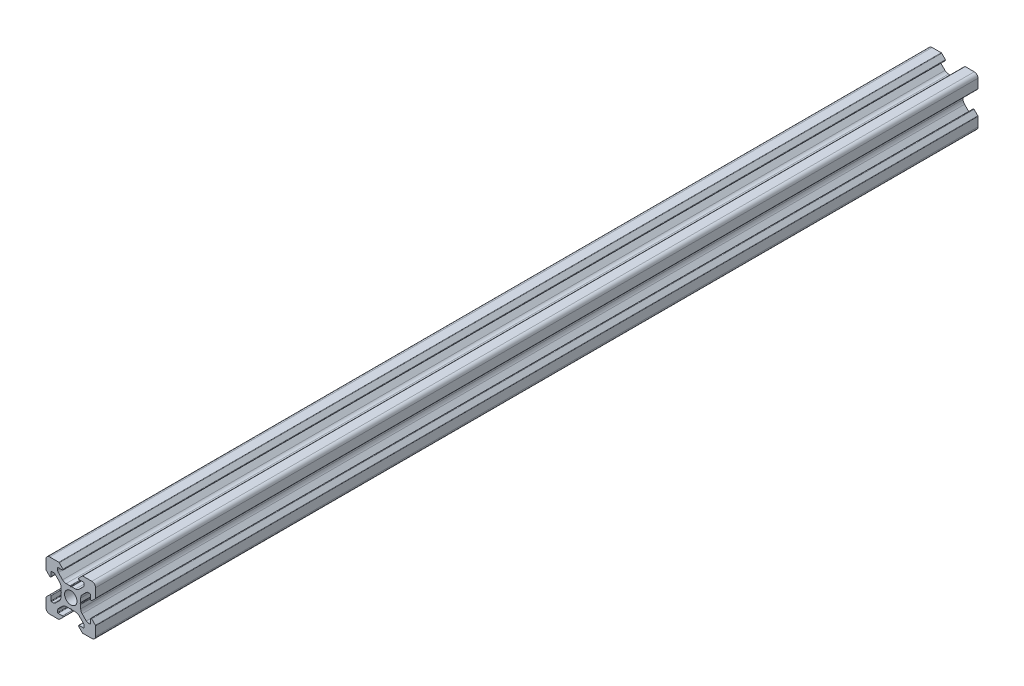
SolidWorks part; units mm, degrees
material "6063-T5"
ref_plane "Спереди" through (0, 0, 0) normal (0, 0, 1) x (1, 0, 0)
ref_plane "Сверху" through (0, 0, 0) normal (0, 1, 0) x (1, 0, 0)
ref_plane "Справа" through (0, 0, 0) normal (1, 0, 0) x (0, 0, -1)
sketch "Model" plane through (0, 0, 0) normal (0, 0, 1) x (1, 0, 0)
  line L0 (-4, 0.3377) -> (-4, 1.8988)
  line L1 (-4.5858, 3.313) -> (-6.2799, 5.0071)
  line L2 (-6.987, 5.3) -> (-7.8, 5.3)
  line L3 (-8, 5.1) -> (-8, 3.33)
  line L4 (-9.9268, 4.6532) -> (-8.4268, 3.1532)
  line L5 (-10, 4.83) -> (-10, 8.5)
  line L6 (-4.6532, 9.9268) -> (-3.1532, 8.4268)
  line L7 (-0.1815, 3.9452) -> (0, 3.8)
  line L8 (0.1815, 3.9452) -> (0, 3.8)
  line L9 (0.3377, 4) -> (1.8988, 4)
  line L10 (3.313, 4.5858) -> (5.0071, 6.2799)
  line L11 (5.3, 6.987) -> (5.3, 7.8)
  line L12 (5.1, 8) -> (3.33, 8)
  line L13 (4.6532, 9.9268) -> (3.1532, 8.4268)
  line L14 (4.83, 10) -> (8.5, 10)
  line L15 (10, 4.83) -> (10, 8.5)
  line L16 (9.9268, 4.6532) -> (8.4268, 3.1532)
  line L17 (8, 5.1) -> (8, 3.33)
  line L18 (6.987, 5.3) -> (7.8, 5.3)
  line L19 (4.5858, 3.313) -> (6.2799, 5.0071)
  line L20 (4, 0.3377) -> (4, 1.8988)
  line L21 (3.9452, 0.1815) -> (3.8, 0)
  line L22 (3.9452, -0.1815) -> (3.8, 0)
  line L23 (4, -0.3377) -> (4, -1.8988)
  line L24 (4.5858, -3.313) -> (6.2799, -5.0071)
  line L25 (6.987, -5.3) -> (7.8, -5.3)
  line L26 (8, -5.1) -> (8, -3.33)
  line L27 (9.9268, -4.6532) -> (8.4268, -3.1532)
  line L28 (10, -4.83) -> (10, -8.5)
  line L29 (4.83, -10) -> (8.5, -10)
  line L30 (4.6532, -9.9268) -> (3.1532, -8.4268)
  line L31 (5.1, -8) -> (3.33, -8)
  line L32 (5.3, -6.987) -> (5.3, -7.8)
  line L33 (3.313, -4.5858) -> (5.0071, -6.2799)
  line L34 (0.3377, -4) -> (1.8988, -4)
  line L35 (0.1815, -3.9452) -> (0, -3.8)
  line L36 (-0.1815, -3.9452) -> (0, -3.8)
  line L37 (-3.313, -4.5858) -> (-5.0071, -6.2799)
  line L38 (-5.3, -6.987) -> (-5.3, -7.8)
  line L39 (-5.1, -8) -> (-3.33, -8)
  line L40 (-4.6532, -9.9268) -> (-3.1532, -8.4268)
  line L41 (-4.83, -10) -> (-8.5, -10)
  line L42 (-10, -4.83) -> (-10, -8.5)
  line L43 (-9.9268, -4.6532) -> (-8.4268, -3.1532)
  line L44 (-8, -5.1) -> (-8, -3.33)
  line L45 (-6.987, -5.3) -> (-7.8, -5.3)
  line L46 (-4.5858, -3.313) -> (-6.2799, -5.0071)
  line L47 (-4, -0.3377) -> (-4, -1.8988)
  line L48 (-3.9452, -0.1815) -> (-3.8, 0)
  line L49 (-3.9452, 0.1815) -> (-3.8, 0)
  line L50 (-0.3377, -4) -> (-1.8988, -4)
  line L51 (-0.3377, 4) -> (-1.8988, 4)
  line L52 (-3.313, 4.5858) -> (-5.0071, 6.2799)
  line L53 (-5.3, 6.987) -> (-5.3, 7.8)
  line L54 (-5.1, 8) -> (-3.33, 8)
  line L55 (-4.83, 10) -> (-8.5, 10)
  arc A0 (-4, 0.3377) -> (-3.9452, 0.1815) centre (-3.75, 0.3377) ccw
  arc A1 (-4, 1.8988) -> (-4.5858, 3.313) centre (-6, 1.8988) ccw
  arc A2 (-6.2799, 5.0071) -> (-6.987, 5.3) centre (-6.987, 4.3) ccw
  arc A3 (-7.8, 5.3) -> (-8, 5.1) centre (-7.8, 5.1) ccw
  arc A4 (-8.4268, 3.1532) -> (-8, 3.33) centre (-8.25, 3.33) ccw
  arc A5 (-10, 4.83) -> (-9.9268, 4.6532) centre (-9.75, 4.83) ccw
  arc A6 (-8.5, 10) -> (-10, 8.5) centre (-8.5, 8.5) ccw
  arc A7 (-4.6532, 9.9268) -> (-4.83, 10) centre (-4.83, 9.75) ccw
  arc A8 (-3.33, 8) -> (-3.1532, 8.4268) centre (-3.33, 8.25) ccw
  arc A9 (-5.1, 8) -> (-5.3, 7.8) centre (-5.1, 7.8) ccw
  arc A10 (-5.3, 6.987) -> (-5.0071, 6.2799) centre (-4.3, 6.987) ccw
  arc A11 (-3.313, 4.5858) -> (-1.8988, 4) centre (-1.8988, 6) ccw
  arc A12 (-0.1815, 3.9452) -> (-0.3377, 4) centre (-0.3377, 3.75) ccw
  arc A13 (0.3377, 4) -> (0.1815, 3.9452) centre (0.3377, 3.75) ccw
  arc A14 (1.8988, 4) -> (3.313, 4.5858) centre (1.8988, 6) ccw
  arc A15 (5.0071, 6.2799) -> (5.3, 6.987) centre (4.3, 6.987) ccw
  arc A16 (5.3, 7.8) -> (5.1, 8) centre (5.1, 7.8) ccw
  arc A17 (3.1532, 8.4268) -> (3.33, 8) centre (3.33, 8.25) ccw
  arc A18 (4.83, 10) -> (4.6532, 9.9268) centre (4.83, 9.75) ccw
  arc A19 (10, 8.5) -> (8.5, 10) centre (8.5, 8.5) ccw
  arc A20 (9.9268, 4.6532) -> (10, 4.83) centre (9.75, 4.83) ccw
  arc A21 (8, 3.33) -> (8.4268, 3.1532) centre (8.25, 3.33) ccw
  arc A22 (8, 5.1) -> (7.8, 5.3) centre (7.8, 5.1) ccw
  arc A23 (6.987, 5.3) -> (6.2799, 5.0071) centre (6.987, 4.3) ccw
  arc A24 (4.5858, 3.313) -> (4, 1.8988) centre (6, 1.8988) ccw
  arc A25 (3.9452, 0.1815) -> (4, 0.3377) centre (3.75, 0.3377) ccw
  arc A26 (4, -0.3377) -> (3.9452, -0.1815) centre (3.75, -0.3377) ccw
  arc A27 (4, -1.8988) -> (4.5858, -3.313) centre (6, -1.8988) ccw
  arc A28 (6.2799, -5.0071) -> (6.987, -5.3) centre (6.987, -4.3) ccw
  arc A29 (7.8, -5.3) -> (8, -5.1) centre (7.8, -5.1) ccw
  arc A30 (8.4268, -3.1532) -> (8, -3.33) centre (8.25, -3.33) ccw
  arc A31 (10, -4.83) -> (9.9268, -4.6532) centre (9.75, -4.83) ccw
  arc A32 (8.5, -10) -> (10, -8.5) centre (8.5, -8.5) ccw
  arc A33 (4.6532, -9.9268) -> (4.83, -10) centre (4.83, -9.75) ccw
  arc A34 (3.33, -8) -> (3.1532, -8.4268) centre (3.33, -8.25) ccw
  arc A35 (5.1, -8) -> (5.3, -7.8) centre (5.1, -7.8) ccw
  arc A36 (5.3, -6.987) -> (5.0071, -6.2799) centre (4.3, -6.987) ccw
  arc A37 (3.313, -4.5858) -> (1.8988, -4) centre (1.8988, -6) ccw
  arc A38 (0.1815, -3.9452) -> (0.3377, -4) centre (0.3377, -3.75) ccw
  arc A39 (-0.3377, -4) -> (-0.1815, -3.9452) centre (-0.3377, -3.75) ccw
  arc A40 (-1.8988, -4) -> (-3.313, -4.5858) centre (-1.8988, -6) ccw
  arc A41 (-5.0071, -6.2799) -> (-5.3, -6.987) centre (-4.3, -6.987) ccw
  arc A42 (-5.3, -7.8) -> (-5.1, -8) centre (-5.1, -7.8) ccw
  arc A43 (-3.1532, -8.4268) -> (-3.33, -8) centre (-3.33, -8.25) ccw
  arc A44 (-4.83, -10) -> (-4.6532, -9.9268) centre (-4.83, -9.75) ccw
  arc A45 (-10, -8.5) -> (-8.5, -10) centre (-8.5, -8.5) ccw
  arc A46 (-9.9268, -4.6532) -> (-10, -4.83) centre (-9.75, -4.83) ccw
  arc A47 (-8, -3.33) -> (-8.4268, -3.1532) centre (-8.25, -3.33) ccw
  arc A48 (-8, -5.1) -> (-7.8, -5.3) centre (-7.8, -5.1) ccw
  arc A49 (-6.987, -5.3) -> (-6.2799, -5.0071) centre (-6.987, -4.3) ccw
  arc A50 (-4.5858, -3.313) -> (-4, -1.8988) centre (-6, -1.8988) ccw
  arc A51 (-3.9452, -0.1815) -> (-4, -0.3377) centre (-3.75, -0.3377) ccw
  circle A52 centre (0, 0) radius 2.5
  dimension "D1" = 20
  dimension "D2" = 20
extrude "Extruded body" add sketch "Model" along normal blind 356
